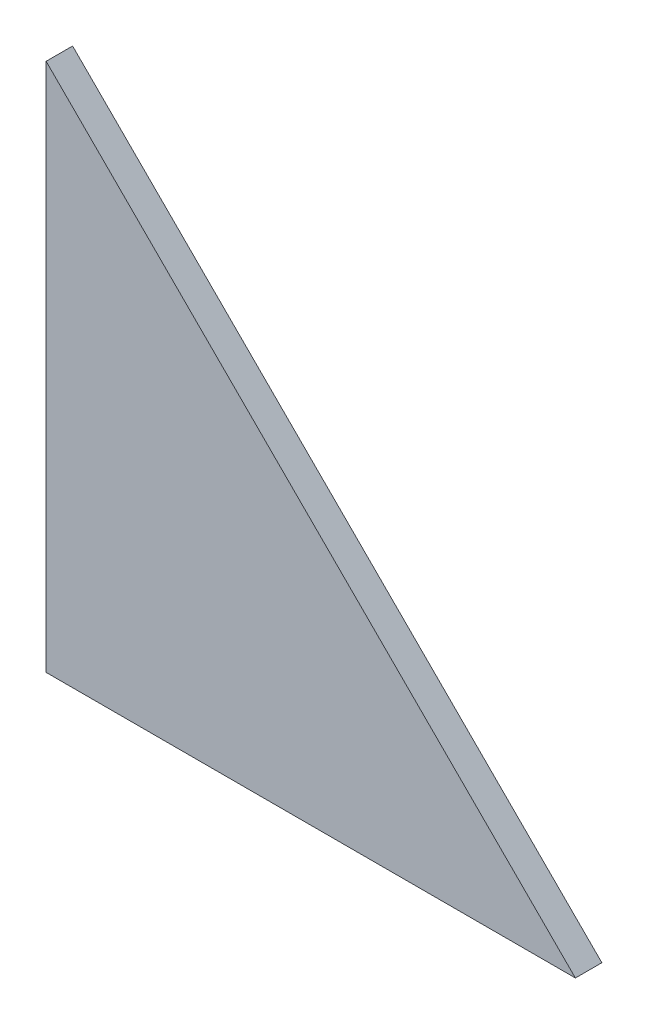
SolidWorks part; units mm, degrees
ref_plane "Front Plane" through (0, 0, 0) normal (0, 0, 1) x (1, 0, 0)
ref_plane "Top Plane" through (0, 0, 0) normal (0, 1, 0) x (1, 0, 0)
ref_plane "Right Plane" through (0, 0, 0) normal (1, 0, 0) x (0, 0, -1)
sketch "Sketch1" plane through (0, 0, 0) normal (0, 0, 1) x (1, 0, 0)
  line L0 (0, 100) -> (100, 0)
  line L2 (0, 100) -> (0, 0)
  line L4 (100, 0) -> (0, 0)
extrude "Boss-Extrude1" add sketch "Sketch1" along normal blind 5
